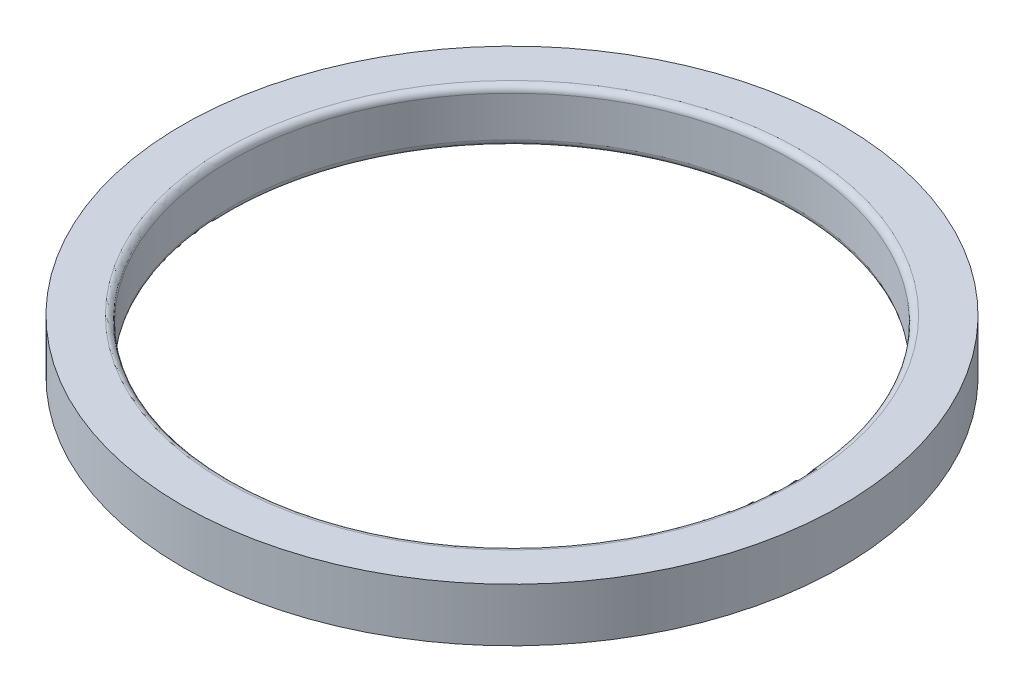
SolidWorks part; units mm, degrees
ref_plane "前视基准面" through (0, 0, 0) normal (0, 0, 1) x (1, 0, 0)
ref_plane "上视基准面" through (0, 0, 0) normal (0, 1, 0) x (1, 0, 0)
ref_plane "右视基准面" through (0, 0, 0) normal (1, 0, 0) x (0, 0, -1)
sketch "草图1" plane through (0, 0, 0) normal (0, 1, 0) x (1, 0, 0)
  circle A0 centre (0, 0) radius 8.7
  circle A1 centre (0, 0) radius 10.2
  dimension "D1" = 17.4
  dimension "D2" = 1.5
extrude "凸台-拉伸1" add sketch "草图1" along normal blind 1.65
fillet "圆角1" radius 0.2 2 edges at (0, 1.65, 8.7) (0, 0, 8.7)
